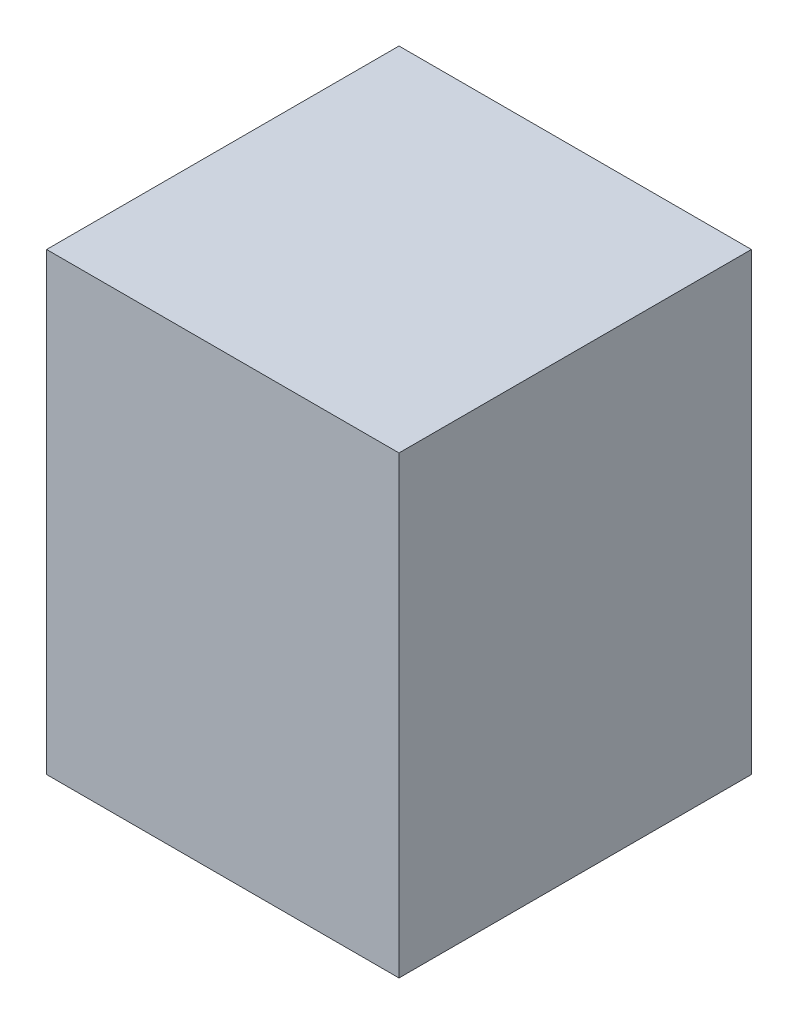
SolidWorks part; units mm, degrees
material "Corrugated Paper"
ref_plane "Front Plane" through (0, 0, 0) normal (0, 0, 1) x (1, 0, 0)
ref_plane "Top Plane" through (0, 0, 0) normal (0, 1, 0) x (1, 0, 0)
ref_plane "Right Plane" through (0, 0, 0) normal (1, 0, 0) x (0, 0, -1)
sketch "Sketch1" plane through (0, 0, 0) normal (0, 1, 0) x (1, 0, 0)
  line L0 (0, 0) -> (0, 304.8)
  line L1 (0, 304.8) -> (304.8, 304.8)
  line L2 (304.8, 304.8) -> (304.8, 0)
  line L3 (304.8, 0) -> (0, 0)
  line L4 (-5.08, -5.08) -> (-5.08, 309.88)
  line L5 (-5.08, 309.88) -> (309.88, 309.88)
  line L6 (309.88, 309.88) -> (309.88, -5.08)
  line L7 (309.88, -5.08) -> (-5.08, -5.08)
  line L8 (304.8, 0) -> (0, 304.8) construction
  line L9 (152.4, 173.863) -> (152.4, 203.2) construction
  line L10 (152.4, 173.863) -> (152.4, 152.4) construction
  line L11 (304.8, 304.8) -> (0, 0) construction
  circle A0 centre (152.4, 188.5315) radius 3.175
  circle A1 centre (188.5315, 152.4) radius 3.175
  circle A2 centre (152.4, 116.2685) radius 3.175
  circle A3 centre (116.2685, 152.4) radius 3.175
  dimension "D1" = 5.08
extrude "Boss-Extrude1" add sketch "Sketch1" along normal blind 406.4 contours L7 L6 L5 L4 L2 L3 L0 L1 | L3 L2 L1 L0 A3 A2 A1 A0 | A3 | A2 | A1 | A0
ref_plane "Plane1" through (0, 190.5, 0) normal (0, 1, 0) x (1, 0, 0)
sketch "Sketch2" plane through (0, 190.5, 0) normal (0, 1, 0) x (1, 0, 0)
  line L0 (0, 0) -> (0, 304.8) construction
  line L3 (0, 152.4) -> (0, 0) construction
  line L8 (0, 152.4) -> (152.4, 152.4) construction
  line L9 (165.1116, 152.4) -> (139.6884, 152.4) construction
  line L10 (165.1116, 152.4) -> (165.1116, -108.2004)
  line L11 (165.1116, -108.2004) -> (139.6884, -108.2004)
  line L12 (139.6884, -108.2004) -> (139.6884, 152.4)
  line L13 (0, 0) -> (139.6884, 0) construction
  line L14 (165.1116, 0) -> (304.8, 0) construction
  line L15 (152.4, 116.5175) -> (152.4, 187.304) construction
  line L17 (-64.6024, 116.5175) -> (152.4, 116.5175)
  line L18 (152.4, 116.5175) -> (342.6825, 116.5175)
  line L19 (152.4, 187.304) -> (152.4, 188.9651) construction
  line L20 (152.4, 188.9651) -> (-64.6024, 188.9651)
  line L21 (-64.6024, 188.9651) -> (-64.6024, 116.5175)
  line L22 (152.4, 188.9651) -> (342.6825, 188.9651)
  line L23 (342.6825, 187.304) -> (342.6825, 116.5175)
  line L24 (342.6825, 188.9651) -> (342.6825, 187.304)
